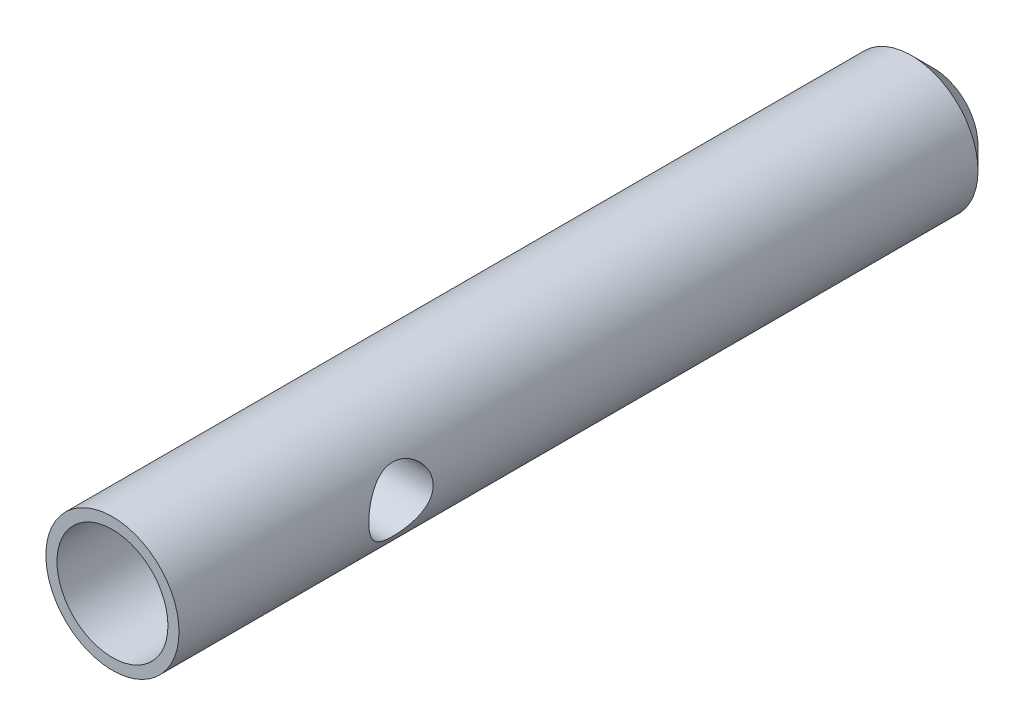
SolidWorks part; units mm, degrees
material "Сплав 2024"
ref_plane "Спереди" through (0, 0, 0) normal (0, 0, 1) x (1, 0, 0)
ref_plane "Сверху" through (0, 0, 0) normal (0, 1, 0) x (1, 0, 0)
ref_plane "Справа" through (0, 0, 0) normal (1, 0, 0) x (0, 0, -1)
sketch "Эскиз1" plane through (0, 0, 0) normal (0, 0, 1) x (1, 0, 0)
  circle A0 centre (0, 0) radius 3
  dimension "D1" = 6
extrude "Бобышка-Вытянуть1" add sketch "Эскиз1" along normal blind 37
sketch "Эскиз2" plane through (0, 0, 37) normal (0, 0, 1) x (1, 0, 0)
  circle A0 centre (0, 0) radius 2.5
  dimension "D1" = 5
extrude "Вырез-Вытянуть1" cut sketch "Эскиз2" against normal blind 6
chamfer "Фаска1" distance 1 angle 45 1 edges at (3, 0, 0)
ref_plane "Плоскость1" through (3, 0, 0) normal (1, 0, 0) x (0, 0, -1)
sketch "Эскиз3" plane through (3, 0, 0) normal (1, 0, 0) x (0, 0, -1)
  line L1 (-37, 3) -> (-37, -3) construction
  line L2 (-27, 5.4441) -> (-27, -6.8987) construction
  line L3 (-37, 0) -> (-1, 0) construction
  line L4 (-1, 3) -> (-1, -3) construction
  dimension "D1" = 10
hole_wizard "Отверстие обработанное метчиком M3.5x0.61" positions "Эскиз5" profile "Эскиз4" tap size "M3.5x0.6" standard "Ansi Metric" end condition through all
sketch "Эскиз5" plane through (3, 0, 0) normal (1, 0, 0) x (0, 0, -1)
  line L0 (-37, 0) -> (-1, 0) construction
  line L1 (-27, 5.4441) -> (-27, -6.8987) construction
  point P0 (-27, 0)
sketch "Эскиз4" plane through (3, 0, 27) normal (0, 1, 0) x (0, 0, -1)
  line L0 (0, 0) -> (0, 6)
  line L1 (0, 6) -> (1.45, 6)
  line L2 (1.45, 6) -> (1.45, 0)
  line L5 (1.45, 0) -> (0, 0)
  line L11 (0, -6.35) -> (0, 107.95) construction
  dimension "Диаметр проходного сверла" = 2.9
  dimension "Глубина проходного сверла" = 6
cosmetic thread "Отверстие резьбы1" parameters "D2"=3.5
